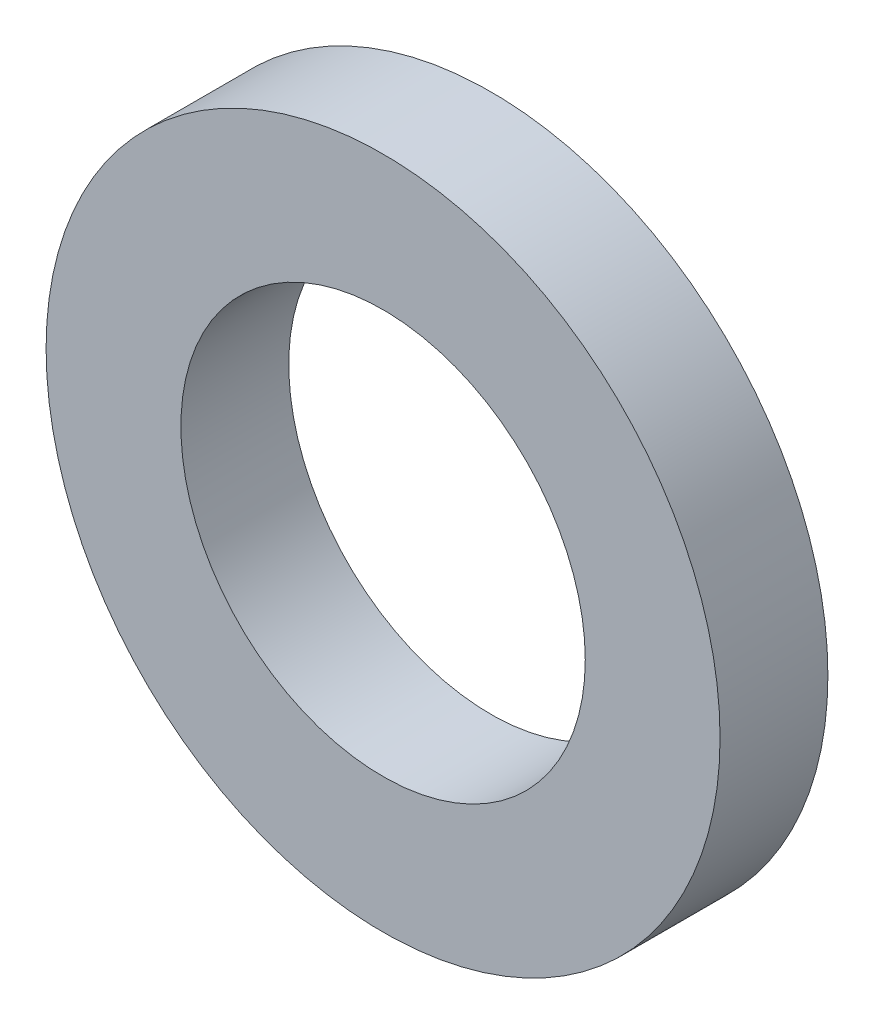
SolidWorks part; units mm, degrees
ref_plane "Front Plane" through (0, 0, 0) normal (0, 0, 1) x (1, 0, 0)
ref_plane "Top Plane" through (0, 0, 0) normal (0, 1, 0) x (1, 0, 0)
ref_plane "Right Plane" through (0, 0, 0) normal (1, 0, 0) x (0, 0, -1)
sketch "Sketch1" plane through (0, 0, 0) normal (0, 0, 1) x (1, 0, 0)
  circle A0 centre (0, 0) radius 2.25
  circle A1 centre (0, 0) radius 3.75
  dimension "D1" = 4.5
  dimension "D2" = 7.5
extrude "Boss-Extrude1" add sketch "Sketch1" along normal blind 1.2
